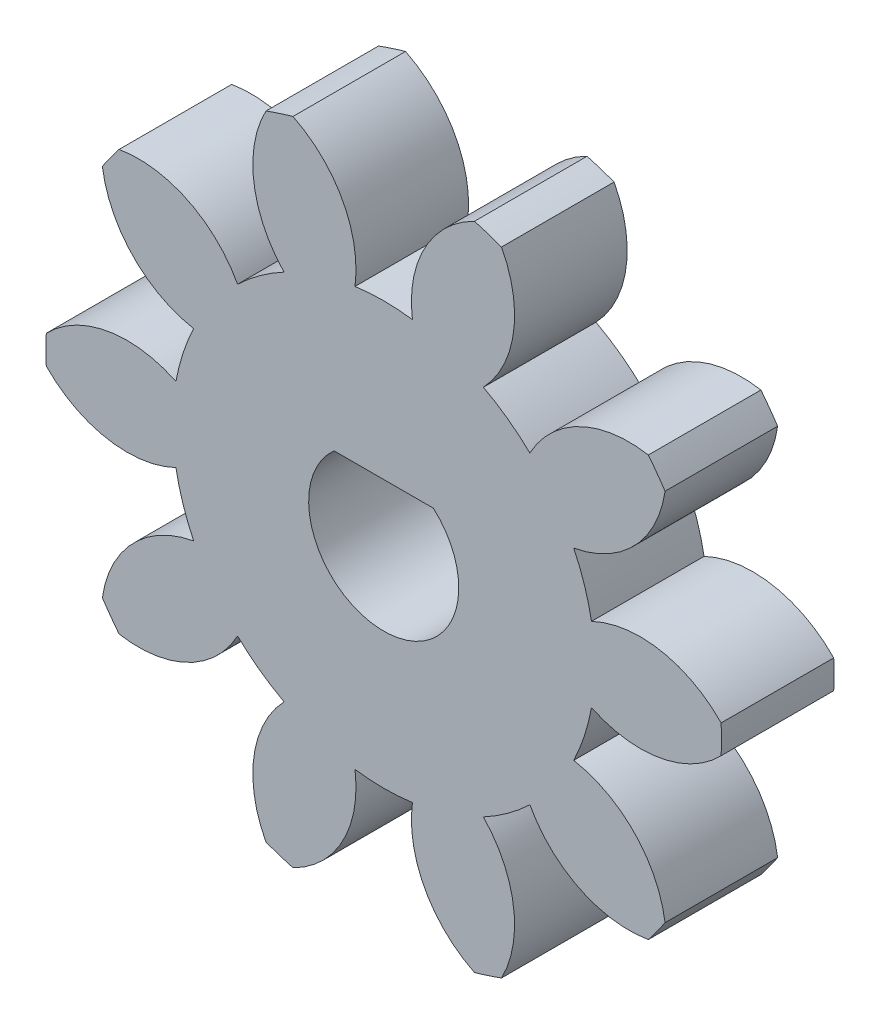
SolidWorks part; units mm, degrees
ref_plane "Front Plane" through (0, 0, 0) normal (0, 0, 1) x (1, 0, 0)
ref_plane "Top Plane" through (0, 0, 0) normal (0, 1, 0) x (1, 0, 0)
ref_plane "Right Plane" through (0, 0, 0) normal (1, 0, 0) x (0, 0, -1)
sketch "Sketch1" plane through (0, 0, 0) normal (0, 0, 1) x (1, 0, 0)
  circle A0 centre (0, 0) radius 9
  dimension "addendumDiameter" = 18
extrude "Boss-Extrude1" add sketch "Sketch1" along normal blind 3
sketch "Sketch2" plane through (0, 0, 3) normal (0, 0, 1) x (1, 0, 0)
  line L0 (0, 0) -> (0, 34.1845) construction
  line L1 (0, 0) -> (-6.0969, 18.7642) construction
  line L2 (-1.1077, 7.4177) -> (-2.2858, 7.035) construction
  circle A0 centre (0, 0) radius 5.625 construction
  circle A1 centre (0, 0) radius 7.0477 construction
  circle A2 centre (0, 0) radius 7.5 construction
  arc A3 (-2.4183, 8.669) -> (2.4183, 8.669) centre (0, 0) cw
  arc A4 (-2.4183, 8.669) -> (-0.765, 5.5727) centre (-3.7379, 5.9748) cw
  circle A5 centre (0, 0) radius 9 construction
  arc A6 (2.4183, 8.669) -> (0.765, 5.5727) centre (3.7379, 5.9748) ccw
  arc A7 (-0.765, 5.5727) -> (0.765, 5.5727) centre (0, 0) cw
  dimension "pitch diameter" = 15
  dimension "dedendum" = 11.25
  dimension "base diameter" = 14.0954
  dimension "D1" = 3
  dimension "D4" = 18
  dimension "D2" = 1.1781
extrude "Cut-Extrude1" cut sketch "Sketch2" against normal through all
pattern_circular "CirPattern1" count 10 every 36 about axis through (0, 0, 0) along (0, 0, 1) of "Cut-Extrude1"
sketch "Sketch3" plane through (0, 0, 3) normal (0, 0, 1) x (1, 0, 0)
  line L0 (0, 0) -> (0, 17.5) construction
  line L1 (-5.2992, 16.6784) -> (0, 7.5)
  line L2 (0, 7.5) -> (5.2992, 16.6784)
  arc A0 (-5.2992, 16.6784) -> (5.2992, 16.6784) centre (0, 0) cw
  dimension "D1" = 17.5
  dimension "D2" = 60
  dimension "D3" = 10
extrude "Cut-Extrude2" [suppressed] cut sketch "Sketch3" against normal through all
fillet "Fillet1" [suppressed] radius 1
fillet "Fillet2" [suppressed] radius 1
fillet "Fillet3" [suppressed] radius 1
pattern_circular "CirPattern2" [suppressed] count 6 over 360
sketch "Sketch4" plane through (0, 0, 3) normal (0, 0, 1) x (1, 0, 0)
  line L0 (-1.3229, 1.5) -> (1.3229, 1.5)
  line L1 (0, 1.5) -> (0, 0) construction
  arc A0 (-1.3229, 1.5) -> (1.3229, 1.5) centre (0, 0) ccw
  dimension "D2" = 2
  dimension "D1" = 1.5
extrude "Cut-Extrude3" cut sketch "Sketch4" against normal through all
equation "\"module\"= 1.5"
equation "\"teeth\"= 10"
equation "\"pressureAngle\"= 20deg"
equation "\"gearThickness\"= 3"
equation "\"addendumFactor\"= 1"
equation "\"dedendumFactor\"= 1.25"
equation "\"pitch\"= 1 / \"module\""
equation "\"pitchDiameter\"= \"teeth\" / \"pitch\""
equation "\"addendum\"= \"addendumFactor\"/\"pitch\""
equation "\"dedendum\"= \"dedendumFactor\" / \"pitch\""
equation "\"D1@Boss-Extrude1\"=\"gearThickness\""
equation "\"dedendum@Sketch2\" = \"pitchDiameter\" - 2 * \"dedendum\""
equation "\"base diameter@Sketch2\" = \"pitchDiameter\" * cos ( \"pressureAngle\" ) "
equation "\"pitch diameter@Sketch2\" = \"pitchDiameter\""
equation "\"D4@Sketch2\"= 180 / \"teeth\""
equation "\"D1@Sketch2\"=\"pitchDiameter\"/5"
equation "\"D2@Sketch2\"=PI / 2 / \"pitch\" / 2"
equation "\"D1@CirPattern1\"= \"teeth\""
equation "\"D2@CirPattern1\"= 360 / \"teeth\""
equation "\"addendumDiameter@Sketch1\"=\"pitchDiameter\"+2 * \"addendum\""
